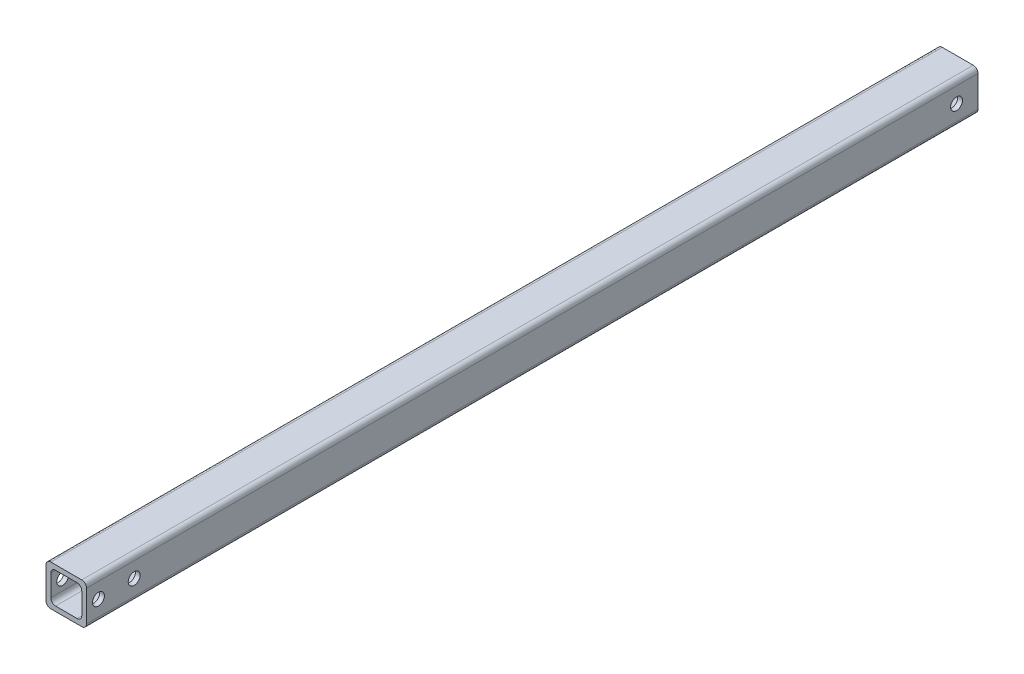
SolidWorks part; units mm, degrees
ref_plane "Front Plane" through (0, 0, 0) normal (0, 0, 1) x (1, 0, 0)
ref_plane "Top Plane" through (0, 0, 0) normal (0, 1, 0) x (1, 0, 0)
ref_plane "Right Plane" through (0, 0, 0) normal (1, 0, 0) x (0, 0, -1)
sketch "Sketch1" plane through (0, 0, 0) normal (0, 0, 1) x (1, 0, 0)
  line L1 (-48.135, 23.5346) -> (-31.135, 23.5346)
  line L2 (-48.135, 23.5346) -> (-48.135, 6.5346)
  line L3 (-48.135, 6.5346) -> (-31.135, 6.5346)
  line L4 (-31.135, 23.5346) -> (-31.135, 6.5346)
  dimension "D1" = 17
  dimension "D2" = 17
extrude "Extrude1" add sketch "Sketch1" along normal blind 374
fillet "Fillet2" radius 2 4 edges at (-48.135, 6.5346, 187) (-31.135, 6.5346, 187) (-48.135, 23.5346, 187) (-31.135, 23.5346, 187)
sketch "Sketch2" plane through (0, 0, 374) normal (0, 0, 1) x (1, 0, 0)
  line L0 (-48.135, 21.5346) -> (-48.135, 8.5346) construction
  line L1 (-46.135, 21.5346) -> (-33.135, 21.5346)
  line L2 (-46.135, 21.5346) -> (-46.135, 8.5346)
  line L3 (-46.135, 8.5346) -> (-33.135, 8.5346)
  line L4 (-33.135, 21.5346) -> (-33.135, 8.5346)
  line L5 (-33.135, 23.5346) -> (-46.135, 23.5346) construction
  dimension "D1" = 13
  dimension "D2" = 13
  dimension "D3" = 2
  dimension "D4" = 2
extrude "Extrude2" cut sketch "Sketch2" against normal through all
fillet "Fillet3" radius 2 4 edges at (-33.135, 8.5346, 187) (-46.135, 8.5346, 187) (-46.135, 21.5346, 187) (-33.135, 21.5346, 187)
sketch "Sketch3" plane through (-31.135, 0, 0) normal (1, 0, 0) x (0, 0, -1)
  line L0 (-374, 8.5346) -> (-374, 21.5346) construction
  line L1 (0, 8.5346) -> (0, 21.5346) construction
  circle A0 centre (-369, 15.0346) radius 2.5
  circle A1 centre (-354, 15.0346) radius 2.5
  circle A2 centre (-9, 15.0346) radius 2.5
  point P8 (0, 15.0346)
  dimension "D1" = 5
  dimension "D2" = 5
  dimension "D3" = 5
  dimension "D4" = 5
  dimension "D5" = 15
  dimension "D6" = 9
extrude "Extrude3" cut sketch "Sketch3" against normal through all
